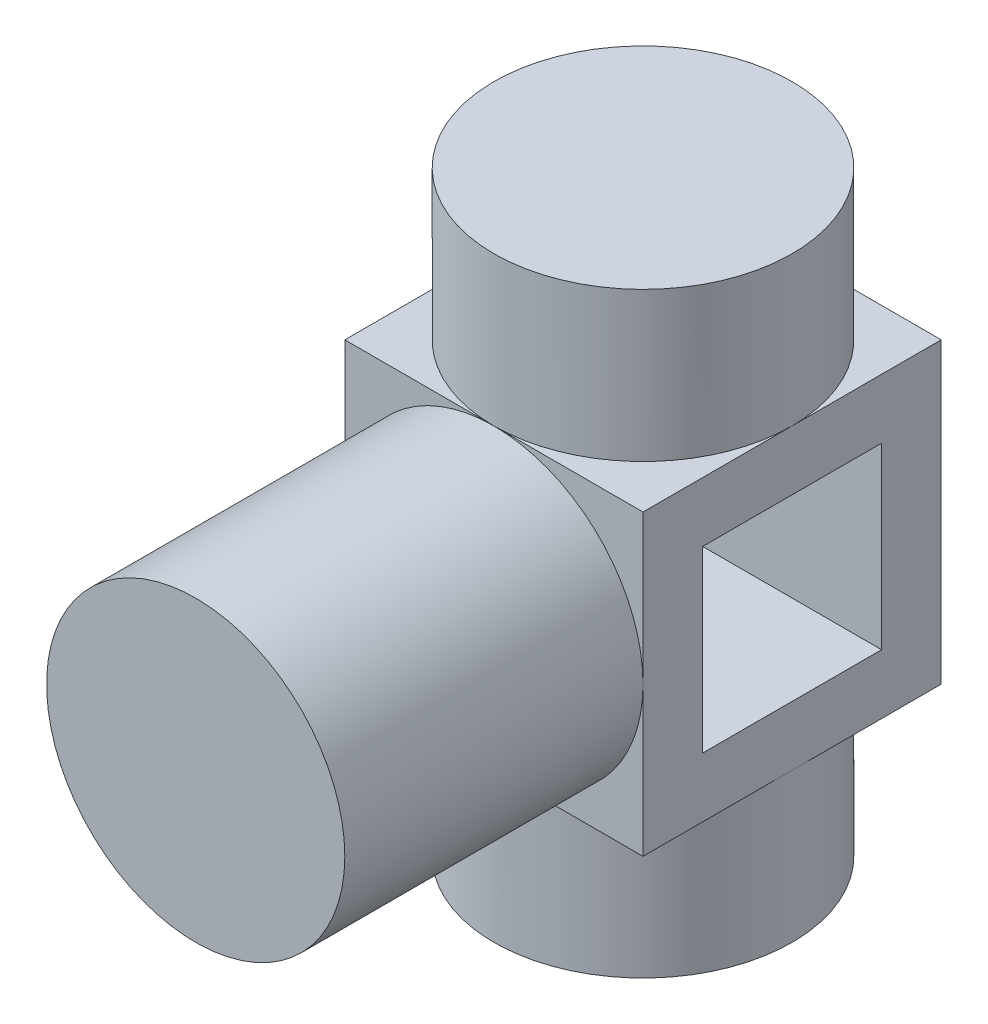
SolidWorks part; units mm, degrees
ref_plane "Front Plane" through (0, 0, 0) normal (0, 0, 1) x (1, 0, 0)
ref_plane "Top Plane" through (0, 0, 0) normal (0, 1, 0) x (1, 0, 0)
ref_plane "Right Plane" through (0, 0, 0) normal (1, 0, 0) x (0, 0, -1)
sketch "Sketch1" plane through (0, 0, 0) normal (0, 1, 0) x (1, 0, 0)
  line L1 (-25, 25) -> (25, 25)
  line L2 (-25, 25) -> (-25, -25)
  line L3 (-25, -25) -> (25, -25)
  line L4 (25, 25) -> (25, -25)
  line L5 (-25, 25) -> (25, -25) construction
  line L6 (-25, -25) -> (25, 25) construction
  point P0 (0, 0)
  dimension "D1" = 50
  dimension "D2" = 50
extrude "Boss-Extrude1" add sketch "Sketch1" along normal blind 100
sketch "Sketch2" plane through (0, 0, 25) normal (0, 0, 1) x (1, 0, 0)
  line L0 (-25, 50) -> (25, 50) construction
  line L1 (-25, 100) -> (-25, 0) construction
  line L2 (25, 100) -> (25, 0) construction
  line L4 (-25, 75) -> (25, 75)
  line L5 (-25, 75) -> (-25, 25)
  line L6 (-25, 25) -> (25, 25)
  line L7 (25, 75) -> (25, 25)
  line L8 (-25, 75) -> (25, 25) construction
  line L9 (-25, 25) -> (25, 75) construction
  point P6 (0, 50)
  dimension "D1" = 50
  dimension "D2" = 50
extrude "Boss-Extrude2" add sketch "Sketch2" along normal blind 50
sketch "Sketch3" plane through (0, 0, 75) normal (0, 0, 1) x (1, 0, 0)
  line L0 (0, 75) -> (0, 25) construction
  line L1 (25, 75) -> (-25, 75) construction
  line L2 (-25, 25) -> (25, 25) construction
  line L4 (-25, 75) -> (25, 75)
  line L5 (-25, 75) -> (-25, 25)
  line L6 (-25, 25) -> (25, 25)
  line L7 (25, 75) -> (25, 25)
  line L8 (-25, 75) -> (25, 25) construction
  line L9 (-25, 25) -> (25, 75) construction
  circle A0 centre (0, 50) radius 25
  line M1 (25, 25) -> (25, 75)
  line M2 (25, 75) -> (-25, 75)
  line M3 (-25, 75) -> (-25, 25)
  line M4 (-25, 25) -> (25, 25)
extrude "Cut-Extrude1" cut sketch "Sketch3" against normal blind 50 contours A0 L4 M3 | A0 L7 M2 | A0 L6 M1 | A0 L5 M4
sketch "Sketch4" plane through (0, 100, 0) normal (0, 1, 0) x (1, 0, 0)
  line L0 (0, 25) -> (0, -25) construction
  line L1 (25, 25) -> (-25, 25) construction
  line L2 (-25, -25) -> (25, -25) construction
  line L4 (-25, 25) -> (25, 25)
  line L5 (-25, 25) -> (-25, -25)
  line L6 (-25, -25) -> (25, -25)
  line L7 (25, 25) -> (25, -25)
  line L8 (-25, 25) -> (25, -25) construction
  line L9 (-25, -25) -> (25, 25) construction
  circle A0 centre (0, 0) radius 25
  point P6 (0, 0)
  line M6 (25, -25) -> (25, 25)
  line M7 (25, 25) -> (-25, 25)
  line M8 (-25, 25) -> (-25, -25)
  line M9 (-25, -25) -> (25, -25)
extrude "Cut-Extrude3" cut sketch "Sketch4" against normal blind 25 contours A0 L5 M9 | A0 L4 M8 | A0 L7 M7 | A0 L6 M6
sketch "Sketch5" plane through (0, 0, 0) normal (0, -1, 0) x (1, 0, 0)
  line L1 (-25, 25) -> (25, 25)
  line L2 (-25, 25) -> (-25, -25)
  line L3 (-25, -25) -> (25, -25)
  line L4 (25, 25) -> (25, -25)
  line L5 (-25, 25) -> (25, -25) construction
  line L6 (-25, -25) -> (25, 25) construction
  circle A0 centre (0, 0) radius 25
  point P0 (0, 0)
  line M1 (25, -25) -> (25, 25)
  line M2 (25, 25) -> (-25, 25)
  line M3 (-25, 25) -> (-25, -25)
  line M4 (-25, -25) -> (25, -25)
extrude "Cut-Extrude4" cut sketch "Sketch5" against normal blind 25 contours A0 L1 M3 | A0 L4 M2 | A0 L3 M1 | A0 L2 M4
sketch "Sketch6" plane through (-25, 0, 0) normal (-1, 0, 0) x (0, 0, 1)
  line L0 (-25, 50) -> (25, 50) construction
  line L1 (-25, 75) -> (-25, 25) construction
  line L3 (-15, 65) -> (15, 65)
  line L4 (-15, 65) -> (-15, 35)
  line L5 (-15, 35) -> (15, 35)
  line L6 (15, 65) -> (15, 35)
  line L7 (-15, 65) -> (15, 35) construction
  line L8 (-15, 35) -> (15, 65) construction
  point P5 (0, 50)
  dimension "D1" = 30
  dimension "D2" = 30
extrude "Cut-Extrude5" cut sketch "Sketch6" against normal up to next
